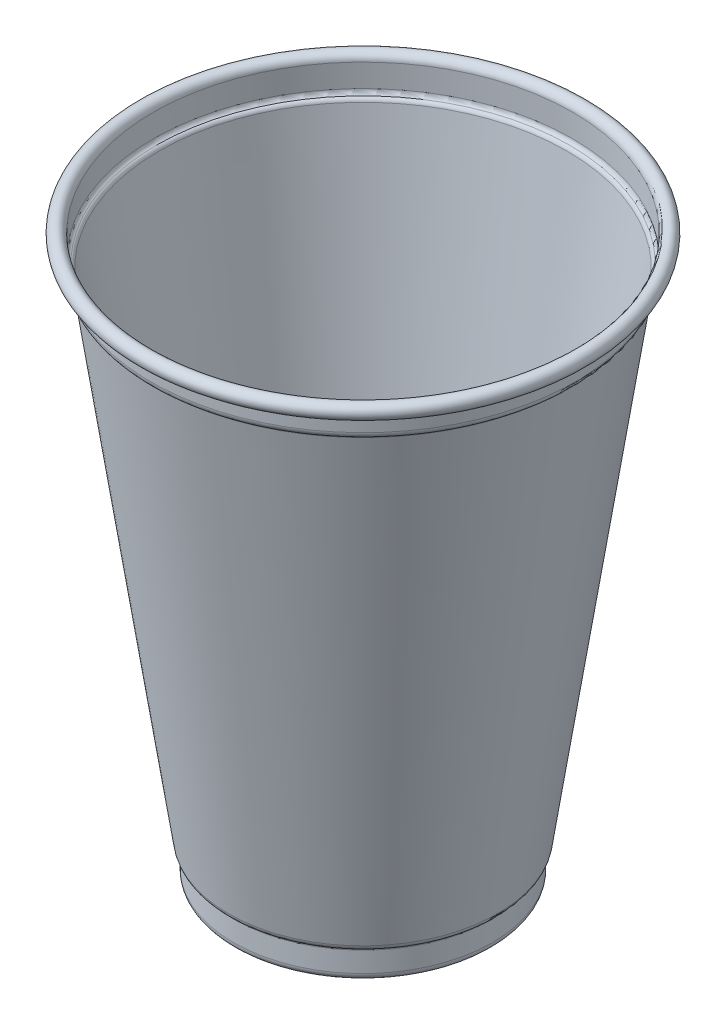
SolidWorks part; units mm, degrees
material "ABS"
ref_plane "Front Plane" through (0, 0, 0) normal (0, 0, 1) x (1, 0, 0)
ref_plane "Top Plane" through (0, 0, 0) normal (0, 1, 0) x (1, 0, 0)
ref_plane "Right Plane" through (0, 0, 0) normal (1, 0, 0) x (0, 0, -1)
sketch "Sketch1" plane through (0, 0, 0) normal (0, 0, 1) x (1, 0, 0)
  line L0 (0, 0) -> (0, 120) construction
  line L1 (0, 0) -> (-27.15, 0) construction
  line L2 (0, 120) -> (-44.75, 120) construction
  line L3 (-44.75, 120) -> (-27.15, 0) construction
  line L4 (0, 0.85) -> (0, 0.35)
  line L5 (-138.8782, 6.3) -> (102.1067, 6.3) construction
  line L6 (-44.75, 112.7) -> (-44.5434, 112.7)
  line L7 (-44.75, 118.4352) -> (-44.75, 113.5359)
  line L8 (0, 112.7) -> (92.9138, 112.7) construction
  line L9 (-27, 21.6357) -> (-27, 1.6227) construction
  line L10 (-27.0244, 5.2762) -> (-27.1256, 1.0238)
  line L11 (-28.0241, 6.3) -> (-28.074, 6.3)
  line L12 (-28.1722, 6.9693) -> (-43.554, 111.8451)
  line L13 (-19.35, 3.2022) -> (-19.35, -1.2732) construction
  line L14 (-19.1095, 0.1474) -> (-18.2034, 0.7026)
  line L15 (-26.1259, 0) -> (-19.632, 0)
  line L16 (-17.6809, 0.85) -> (0, 0.85)
  line L17 (-45.25, 118.4352) -> (-45.25, 113.5359)
  line L18 (-28.6669, 6.8968) -> (-44.0487, 111.7726)
  line L19 (-27.5242, 5.2881) -> (-27.6255, 1.0357)
  line L20 (-26.1259, -0.5) -> (-19.632, -0.5)
  line L21 (-18.8483, -0.279) -> (-17.9422, 0.2763)
  line L22 (-17.6809, 0.35) -> (0, 0.35)
  line L23 (-45.8269, 117.4996) -> (-45.6005, 117.0538)
  arc A0 (-44.75, 118.4352) -> (-45.6005, 117.0538) centre (-46.2971, 118.4352) ccw
  arc A1 (-27.1256, 1.0238) -> (-26.1259, 0) centre (-26.1259, 1) ccw
  arc A2 (-19.632, 0) -> (-19.1095, 0.1474) centre (-19.632, 1) ccw
  arc A3 (-18.2034, 0.7026) -> (-17.6809, 0.85) centre (-17.6809, -0.15) cw
  arc A4 (-27.6034, 6.2072) -> (-27.0244, 5.2762) centre (-28.0241, 5.3) cw
  arc A5 (-44.1467, 112.618) -> (-43.554, 111.8451) centre (-44.5434, 111.7) cw
  arc A6 (-28.1722, 6.9693) -> (-27.6034, 6.2072) centre (-27.1828, 7.1144) ccw
  arc A7 (-44.75, 113.5359) -> (-44.1467, 112.618) centre (-43.75, 113.5359) ccw
  arc A8 (-45.25, 118.4352) -> (-45.8269, 117.4996) centre (-46.2971, 118.4352) ccw
  arc A9 (-45.25, 113.5359) -> (-44.345, 112.159) centre (-43.75, 113.5359) ccw
  arc A10 (-44.345, 112.159) -> (-44.0487, 111.7726) centre (-44.5434, 111.7) cw
  arc A11 (-28.6669, 6.8968) -> (-27.8138, 5.7536) centre (-27.1828, 7.1144) ccw
  arc A12 (-27.8138, 5.7536) -> (-27.5242, 5.2881) centre (-28.0241, 5.3) cw
  arc A13 (-27.6255, 1.0357) -> (-26.1259, -0.5) centre (-26.1259, 1) ccw
  arc A14 (-19.632, -0.5) -> (-18.8483, -0.279) centre (-19.632, 1) ccw
  arc A15 (-17.9422, 0.2763) -> (-17.6809, 0.35) centre (-17.6809, -0.15) cw
  arc A17 (-45.25, 118.4352) -> (-45.5611, 117.6904) centre (-46.2971, 118.4352) ccw construction
  arc A19 (-44.75, 118.4352) -> (-45.2096, 117.3348) centre (-46.2971, 118.4352) ccw construction
  point P30 (-19.35, 0)
  point P35 (-27, 6.3)
  point P38 (-43.6793, 112.7)
  dimension "D4" = 1
  dimension "D9" = 1
  dimension "D10" = 1
  dimension "D11" = 1
  dimension "D1" = 120
  dimension "D2" = 27.15
  dimension "D3" = 44.75
  dimension "D5" = 6.3
  dimension "D6" = 7.3
  dimension "D7" = 27
  dimension "D8" = 19.35
  dimension "D12" = 0.5
revolve "Revolve2" add sketch "Sketch1" angle 360 about L0
